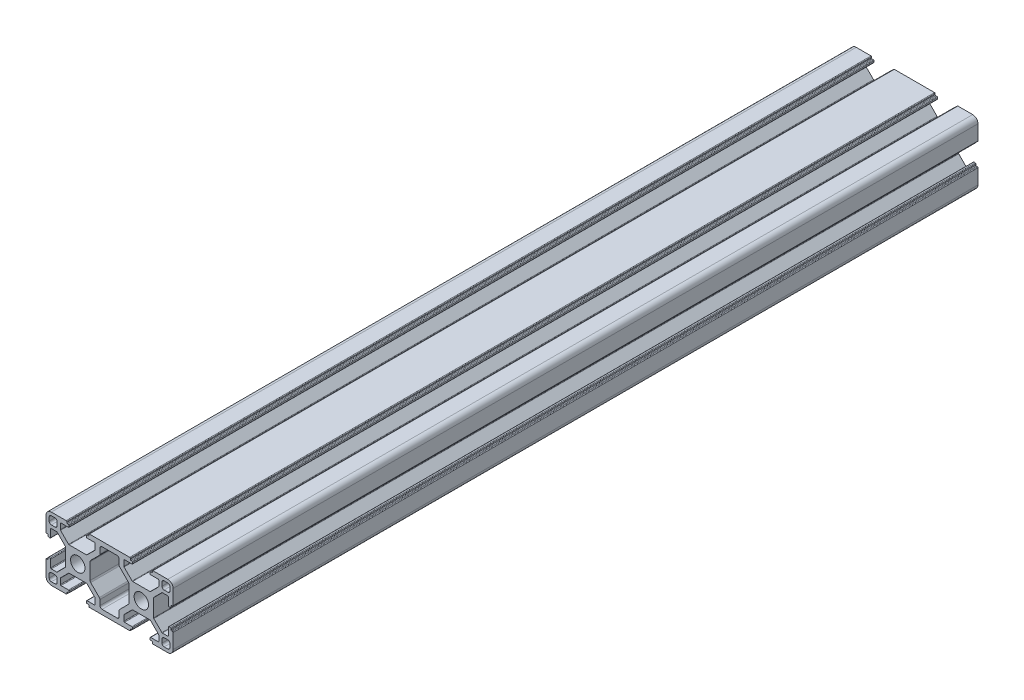
SolidWorks part; units mm, degrees
ref_plane "前视基准面" through (0, 0, 0) normal (0, 0, 1) x (1, 0, 0)
ref_plane "上视基准面" through (0, 0, 0) normal (0, 1, 0) x (1, 0, 0)
ref_plane "右视基准面" through (0, 0, 0) normal (1, 0, 0) x (0, 0, -1)
sketch "Model" plane through (0, 0, 0) normal (0, 0, 1) x (1, 0, 0)
  line L0 (154.3439, 58.7492) -> (156.0939, 58.7492)
  line L1 (157.0939, 57.7492) -> (157.0939, 55.9992)
  line L2 (156.0939, 54.9992) -> (154.3439, 54.9992)
  line L3 (153.3439, 55.9992) -> (153.3439, 57.7492)
  line L4 (102.8439, 58.7492) -> (101.0939, 58.7492)
  line L5 (100.0939, 57.7492) -> (100.0939, 55.9992)
  line L6 (101.0939, 54.9992) -> (102.8439, 54.9992)
  line L7 (103.8439, 55.9992) -> (103.8439, 57.7492)
  line L8 (147.9939, 59.2492) -> (148.4939, 59.2492)
  line L9 (148.7939, 59.5492) -> (148.7939, 59.9492)
  line L10 (149.0939, 60.2492) -> (156.0939, 60.2492)
  line L11 (158.5939, 57.7492) -> (158.5939, 50.7492)
  line L12 (158.2939, 50.4492) -> (157.8939, 50.4492)
  line L13 (157.5939, 50.1492) -> (157.5939, 49.6492)
  line L14 (157.2939, 49.3492) -> (156.6939, 49.3492)
  line L15 (156.3939, 49.6492) -> (156.3939, 53.1992)
  line L16 (156.0939, 53.4992) -> (153.5238, 53.4992)
  line L17 (153.3117, 53.4113) -> (149.4818, 49.5814)
  line L18 (149.3939, 49.3693) -> (149.3939, 45.2492)
  line L19 (149.3939, 45.2492) -> (149.3939, 41.1291)
  line L20 (149.4818, 40.9169) -> (153.3117, 37.087)
  line L21 (153.5238, 36.9992) -> (156.0939, 36.9992)
  line L22 (156.3939, 37.2992) -> (156.3939, 40.8492)
  line L23 (156.6939, 41.1492) -> (157.2939, 41.1492)
  line L24 (157.5939, 40.8492) -> (157.5939, 40.3492)
  line L25 (157.8939, 40.0492) -> (158.2939, 40.0492)
  line L26 (158.5939, 39.7492) -> (158.5939, 32.7492)
  line L27 (156.0939, 30.2492) -> (149.0939, 30.2492)
  line L28 (148.7939, 30.5492) -> (148.7939, 30.9492)
  line L29 (148.4939, 31.2492) -> (147.9939, 31.2492)
  line L30 (147.6939, 31.5492) -> (147.6939, 32.1492)
  line L31 (147.9939, 32.4492) -> (151.5439, 32.4492)
  line L32 (151.8439, 32.7492) -> (151.8439, 35.3193)
  line L33 (151.756, 35.5314) -> (147.9261, 39.3613)
  line L34 (147.714, 39.4492) -> (143.5939, 39.4492)
  line L35 (143.5939, 39.4492) -> (139.4738, 39.4492)
  line L36 (139.2617, 39.3613) -> (135.4318, 35.5314)
  line L37 (135.3439, 35.3193) -> (135.3439, 32.7492)
  line L38 (135.6439, 32.4492) -> (139.1939, 32.4492)
  line L39 (139.4939, 32.1492) -> (139.4939, 31.5492)
  line L40 (139.1939, 31.2492) -> (138.6939, 31.2492)
  line L41 (138.3939, 30.9492) -> (138.3939, 30.5492)
  line L42 (138.0939, 30.2492) -> (119.0939, 30.2492)
  line L43 (118.7939, 30.5492) -> (118.7939, 30.9492)
  line L44 (118.4939, 31.2492) -> (117.9939, 31.2492)
  line L45 (117.6939, 31.5492) -> (117.6939, 32.1492)
  line L46 (117.9939, 32.4492) -> (121.5439, 32.4492)
  line L47 (121.8439, 32.7492) -> (121.8439, 35.3193)
  line L48 (121.756, 35.5314) -> (117.9261, 39.3613)
  line L49 (117.714, 39.4492) -> (113.5939, 39.4492)
  line L50 (113.5939, 39.4492) -> (109.4738, 39.4492)
  line L51 (109.2617, 39.3613) -> (105.4318, 35.5314)
  line L52 (105.3439, 35.3193) -> (105.3439, 32.7492)
  line L53 (105.6439, 32.4492) -> (109.1939, 32.4492)
  line L54 (109.4939, 32.1492) -> (109.4939, 31.5492)
  line L55 (109.1939, 31.2492) -> (108.6939, 31.2492)
  line L56 (108.3939, 30.9492) -> (108.3939, 30.5492)
  line L57 (108.0939, 30.2492) -> (101.0939, 30.2492)
  line L58 (98.5939, 32.7492) -> (98.5939, 39.7492)
  line L59 (98.8939, 40.0492) -> (99.2939, 40.0492)
  line L60 (99.5939, 40.3492) -> (99.5939, 40.8492)
  line L61 (99.8939, 41.1492) -> (100.4939, 41.1492)
  line L62 (100.7939, 40.8492) -> (100.7939, 37.2992)
  line L63 (101.0939, 36.9992) -> (103.664, 36.9992)
  line L64 (103.8761, 37.087) -> (107.706, 40.9169)
  line L65 (107.7939, 41.1291) -> (107.7939, 45.2492)
  line L66 (107.7939, 45.2492) -> (107.7939, 49.3693)
  line L67 (107.706, 49.5814) -> (103.8761, 53.4113)
  line L68 (103.664, 53.4992) -> (101.0939, 53.4992)
  line L69 (100.7939, 53.1992) -> (100.7939, 49.6492)
  line L70 (100.4939, 49.3492) -> (99.8939, 49.3492)
  line L71 (99.5939, 49.6492) -> (99.5939, 50.1492)
  line L72 (99.2939, 50.4492) -> (98.8939, 50.4492)
  line L73 (98.5939, 50.7492) -> (98.5939, 57.7492)
  line L74 (101.0939, 60.2492) -> (108.0939, 60.2492)
  line L75 (108.3939, 59.9492) -> (108.3939, 59.5492)
  line L76 (108.6939, 59.2492) -> (109.1939, 59.2492)
  line L77 (109.4939, 58.9492) -> (109.4939, 58.3492)
  line L78 (109.1939, 58.0492) -> (105.6439, 58.0492)
  line L79 (105.3439, 57.7492) -> (105.3439, 55.1791)
  line L80 (105.4318, 54.9669) -> (109.2617, 51.137)
  line L81 (109.4738, 51.0492) -> (113.5939, 51.0492)
  line L82 (113.5939, 51.0492) -> (117.714, 51.0492)
  line L83 (117.9261, 51.137) -> (121.756, 54.9669)
  line L84 (121.8439, 55.1791) -> (121.8439, 57.7492)
  line L85 (121.5439, 58.0492) -> (117.9939, 58.0492)
  line L86 (117.6939, 58.3492) -> (117.6939, 58.9492)
  line L87 (117.9939, 59.2492) -> (118.4939, 59.2492)
  line L88 (118.7939, 59.5492) -> (118.7939, 59.9492)
  line L89 (119.0939, 60.2492) -> (138.0939, 60.2492)
  line L90 (138.3939, 59.9492) -> (138.3939, 59.5492)
  line L91 (138.6939, 59.2492) -> (139.1939, 59.2492)
  line L92 (139.4939, 58.9492) -> (139.4939, 58.3492)
  line L93 (139.1939, 58.0492) -> (135.6439, 58.0492)
  line L94 (135.3439, 57.7492) -> (135.3439, 55.1791)
  line L95 (135.4318, 54.9669) -> (139.2617, 51.137)
  line L96 (139.4738, 51.0492) -> (143.5939, 51.0492)
  line L97 (143.5939, 51.0492) -> (147.714, 51.0492)
  line L98 (147.9261, 51.137) -> (151.756, 54.9669)
  line L99 (151.8439, 55.1791) -> (151.8439, 57.7492)
  line L100 (151.5439, 58.0492) -> (147.9939, 58.0492)
  line L101 (147.6939, 58.3492) -> (147.6939, 58.9492)
  line L103 (154.3439, 31.7492) -> (156.0939, 31.7492)
  line L104 (157.0939, 32.7492) -> (157.0939, 34.4992)
  line L105 (156.0939, 35.4992) -> (154.3439, 35.4992)
  line L106 (153.3439, 34.4992) -> (153.3439, 32.7492)
  line L108 (119.3939, 49.0793) -> (119.3939, 45.2492)
  line L109 (119.3939, 45.2492) -> (119.3939, 41.419)
  line L110 (119.6868, 40.7119) -> (123.751, 36.6477)
  line L111 (124.0439, 35.9406) -> (124.0439, 33.4492)
  line L112 (125.0439, 32.4492) -> (128.5939, 32.4492)
  line L113 (128.5939, 32.4492) -> (132.1439, 32.4492)
  line L114 (133.1439, 33.4492) -> (133.1439, 35.9406)
  line L115 (133.4368, 36.6477) -> (137.501, 40.7119)
  line L116 (137.7939, 41.419) -> (137.7939, 45.2492)
  line L117 (137.7939, 45.2492) -> (137.7939, 49.0793)
  line L118 (137.501, 49.7864) -> (133.4368, 53.8507)
  line L119 (133.1439, 54.5578) -> (133.1439, 57.0492)
  line L120 (132.1439, 58.0492) -> (128.5939, 58.0492)
  line L121 (128.5939, 58.0492) -> (125.0439, 58.0492)
  line L122 (124.0439, 57.0492) -> (124.0439, 54.5578)
  line L123 (123.751, 53.8507) -> (119.6868, 49.7864)
  line L128 (102.8439, 31.7492) -> (101.0939, 31.7492)
  line L129 (100.0939, 32.7492) -> (100.0939, 34.4992)
  line L130 (101.0939, 35.4992) -> (102.8439, 35.4992)
  line L131 (103.8439, 34.4992) -> (103.8439, 32.7492)
  circle A0 centre (113.5939, 45.2492) radius 3.4
  circle A1 centre (143.5939, 45.2492) radius 3.4
  arc A2 (154.3439, 58.7492) -> (153.3439, 57.7492) centre (154.3439, 57.7492) ccw
  arc A3 (157.0939, 57.7492) -> (156.0939, 58.7492) centre (156.0939, 57.7492) ccw
  arc A4 (156.0939, 54.9992) -> (157.0939, 55.9992) centre (156.0939, 55.9992) ccw
  arc A5 (153.3439, 55.9992) -> (154.3439, 54.9992) centre (154.3439, 55.9992) ccw
  arc A6 (103.8439, 57.7492) -> (102.8439, 58.7492) centre (102.8439, 57.7492) ccw
  arc A7 (101.0939, 58.7492) -> (100.0939, 57.7492) centre (101.0939, 57.7492) ccw
  arc A8 (100.0939, 55.9992) -> (101.0939, 54.9992) centre (101.0939, 55.9992) ccw
  arc A9 (102.8439, 54.9992) -> (103.8439, 55.9992) centre (102.8439, 55.9992) ccw
  arc A10 (148.4939, 59.2492) -> (148.7939, 59.5492) centre (148.4939, 59.5492) ccw
  arc A11 (149.0939, 60.2492) -> (148.7939, 59.9492) centre (149.0939, 59.9492) ccw
  arc A12 (158.5939, 57.7492) -> (156.0939, 60.2492) centre (156.0939, 57.7492) ccw
  arc A13 (158.2939, 50.4492) -> (158.5939, 50.7492) centre (158.2939, 50.7492) ccw
  arc A14 (157.8939, 50.4492) -> (157.5939, 50.1492) centre (157.8939, 50.1492) ccw
  arc A15 (157.2939, 49.3492) -> (157.5939, 49.6492) centre (157.2939, 49.6492) ccw
  arc A16 (156.3939, 49.6492) -> (156.6939, 49.3492) centre (156.6939, 49.6492) ccw
  arc A17 (156.3939, 53.1992) -> (156.0939, 53.4992) centre (156.0939, 53.1992) ccw
  arc A18 (153.5238, 53.4992) -> (153.3117, 53.4113) centre (153.5238, 53.1992) ccw
  arc A19 (149.4818, 49.5814) -> (149.3939, 49.3693) centre (149.6939, 49.3693) ccw
  arc A20 (149.3939, 41.1291) -> (149.4818, 40.9169) centre (149.6939, 41.1291) ccw
  arc A21 (153.3117, 37.087) -> (153.5238, 36.9992) centre (153.5238, 37.2992) ccw
  arc A22 (156.0939, 36.9992) -> (156.3939, 37.2992) centre (156.0939, 37.2992) ccw
  arc A23 (156.6939, 41.1492) -> (156.3939, 40.8492) centre (156.6939, 40.8492) ccw
  arc A24 (157.5939, 40.8492) -> (157.2939, 41.1492) centre (157.2939, 40.8492) ccw
  arc A25 (157.5939, 40.3492) -> (157.8939, 40.0492) centre (157.8939, 40.3492) ccw
  arc A26 (158.5939, 39.7492) -> (158.2939, 40.0492) centre (158.2939, 39.7492) ccw
  arc A27 (156.0939, 30.2492) -> (158.5939, 32.7492) centre (156.0939, 32.7492) ccw
  arc A28 (148.7939, 30.5492) -> (149.0939, 30.2492) centre (149.0939, 30.5492) ccw
  arc A29 (148.7939, 30.9492) -> (148.4939, 31.2492) centre (148.4939, 30.9492) ccw
  arc A30 (147.6939, 31.5492) -> (147.9939, 31.2492) centre (147.9939, 31.5492) ccw
  arc A31 (147.9939, 32.4492) -> (147.6939, 32.1492) centre (147.9939, 32.1492) ccw
  arc A32 (151.5439, 32.4492) -> (151.8439, 32.7492) centre (151.5439, 32.7492) ccw
  arc A33 (151.8439, 35.3193) -> (151.756, 35.5314) centre (151.5439, 35.3193) ccw
  arc A34 (147.9261, 39.3613) -> (147.714, 39.4492) centre (147.714, 39.1492) ccw
  arc A35 (139.4738, 39.4492) -> (139.2617, 39.3613) centre (139.4738, 39.1492) ccw
  arc A36 (135.4318, 35.5314) -> (135.3439, 35.3193) centre (135.6439, 35.3193) ccw
  arc A37 (135.3439, 32.7492) -> (135.6439, 32.4492) centre (135.6439, 32.7492) ccw
  arc A38 (139.4939, 32.1492) -> (139.1939, 32.4492) centre (139.1939, 32.1492) ccw
  arc A39 (139.1939, 31.2492) -> (139.4939, 31.5492) centre (139.1939, 31.5492) ccw
  arc A40 (138.6939, 31.2492) -> (138.3939, 30.9492) centre (138.6939, 30.9492) ccw
  arc A41 (138.0939, 30.2492) -> (138.3939, 30.5492) centre (138.0939, 30.5492) ccw
  arc A42 (118.7939, 30.5492) -> (119.0939, 30.2492) centre (119.0939, 30.5492) ccw
  arc A43 (118.7939, 30.9492) -> (118.4939, 31.2492) centre (118.4939, 30.9492) ccw
  arc A44 (117.6939, 31.5492) -> (117.9939, 31.2492) centre (117.9939, 31.5492) ccw
  arc A45 (117.9939, 32.4492) -> (117.6939, 32.1492) centre (117.9939, 32.1492) ccw
  arc A46 (121.5439, 32.4492) -> (121.8439, 32.7492) centre (121.5439, 32.7492) ccw
  arc A47 (121.8439, 35.3193) -> (121.756, 35.5314) centre (121.5439, 35.3193) ccw
  arc A48 (117.9261, 39.3613) -> (117.714, 39.4492) centre (117.714, 39.1492) ccw
  arc A49 (109.4738, 39.4492) -> (109.2617, 39.3613) centre (109.4738, 39.1492) ccw
  arc A50 (105.4318, 35.5314) -> (105.3439, 35.3193) centre (105.6439, 35.3193) ccw
  arc A51 (105.3439, 32.7492) -> (105.6439, 32.4492) centre (105.6439, 32.7492) ccw
  arc A52 (109.4939, 32.1492) -> (109.1939, 32.4492) centre (109.1939, 32.1492) ccw
  arc A53 (109.1939, 31.2492) -> (109.4939, 31.5492) centre (109.1939, 31.5492) ccw
  arc A54 (108.6939, 31.2492) -> (108.3939, 30.9492) centre (108.6939, 30.9492) ccw
  arc A55 (108.0939, 30.2492) -> (108.3939, 30.5492) centre (108.0939, 30.5492) ccw
  arc A56 (98.5939, 32.7492) -> (101.0939, 30.2492) centre (101.0939, 32.7492) ccw
  arc A57 (98.8939, 40.0492) -> (98.5939, 39.7492) centre (98.8939, 39.7492) ccw
  arc A58 (99.2939, 40.0492) -> (99.5939, 40.3492) centre (99.2939, 40.3492) ccw
  arc A59 (99.8939, 41.1492) -> (99.5939, 40.8492) centre (99.8939, 40.8492) ccw
  arc A60 (100.7939, 40.8492) -> (100.4939, 41.1492) centre (100.4939, 40.8492) ccw
  arc A61 (100.7939, 37.2992) -> (101.0939, 36.9992) centre (101.0939, 37.2992) ccw
  arc A62 (103.664, 36.9992) -> (103.8761, 37.087) centre (103.664, 37.2992) ccw
  arc A63 (107.706, 40.9169) -> (107.7939, 41.1291) centre (107.4939, 41.1291) ccw
  arc A64 (107.7939, 49.3693) -> (107.706, 49.5814) centre (107.4939, 49.3693) ccw
  arc A65 (103.8761, 53.4113) -> (103.664, 53.4992) centre (103.664, 53.1992) ccw
  arc A66 (101.0939, 53.4992) -> (100.7939, 53.1992) centre (101.0939, 53.1992) ccw
  arc A67 (100.4939, 49.3492) -> (100.7939, 49.6492) centre (100.4939, 49.6492) ccw
  arc A68 (99.5939, 49.6492) -> (99.8939, 49.3492) centre (99.8939, 49.6492) ccw
  arc A69 (99.5939, 50.1492) -> (99.2939, 50.4492) centre (99.2939, 50.1492) ccw
  arc A70 (98.5939, 50.7492) -> (98.8939, 50.4492) centre (98.8939, 50.7492) ccw
  arc A71 (101.0939, 60.2492) -> (98.5939, 57.7492) centre (101.0939, 57.7492) ccw
  arc A72 (108.3939, 59.9492) -> (108.0939, 60.2492) centre (108.0939, 59.9492) ccw
  arc A73 (108.3939, 59.5492) -> (108.6939, 59.2492) centre (108.6939, 59.5492) ccw
  arc A74 (109.4939, 58.9492) -> (109.1939, 59.2492) centre (109.1939, 58.9492) ccw
  arc A75 (109.1939, 58.0492) -> (109.4939, 58.3492) centre (109.1939, 58.3492) ccw
  arc A76 (105.6439, 58.0492) -> (105.3439, 57.7492) centre (105.6439, 57.7492) ccw
  arc A77 (105.3439, 55.1791) -> (105.4318, 54.9669) centre (105.6439, 55.1791) ccw
  arc A78 (109.2617, 51.137) -> (109.4738, 51.0492) centre (109.4738, 51.3492) ccw
  arc A79 (117.714, 51.0492) -> (117.9261, 51.137) centre (117.714, 51.3492) ccw
  arc A80 (121.756, 54.9669) -> (121.8439, 55.1791) centre (121.5439, 55.1791) ccw
  arc A81 (121.8439, 57.7492) -> (121.5439, 58.0492) centre (121.5439, 57.7492) ccw
  arc A82 (117.6939, 58.3492) -> (117.9939, 58.0492) centre (117.9939, 58.3492) ccw
  arc A83 (117.9939, 59.2492) -> (117.6939, 58.9492) centre (117.9939, 58.9492) ccw
  arc A84 (118.4939, 59.2492) -> (118.7939, 59.5492) centre (118.4939, 59.5492) ccw
  arc A85 (119.0939, 60.2492) -> (118.7939, 59.9492) centre (119.0939, 59.9492) ccw
  arc A86 (138.3939, 59.9492) -> (138.0939, 60.2492) centre (138.0939, 59.9492) ccw
  arc A87 (138.3939, 59.5492) -> (138.6939, 59.2492) centre (138.6939, 59.5492) ccw
  arc A88 (139.4939, 58.9492) -> (139.1939, 59.2492) centre (139.1939, 58.9492) ccw
  arc A89 (139.1939, 58.0492) -> (139.4939, 58.3492) centre (139.1939, 58.3492) ccw
  arc A90 (135.6439, 58.0492) -> (135.3439, 57.7492) centre (135.6439, 57.7492) ccw
  arc A91 (135.3439, 55.1791) -> (135.4318, 54.9669) centre (135.6439, 55.1791) ccw
  arc A92 (139.2617, 51.137) -> (139.4738, 51.0492) centre (139.4738, 51.3492) ccw
  arc A93 (147.714, 51.0492) -> (147.9261, 51.137) centre (147.714, 51.3492) ccw
  arc A94 (151.756, 54.9669) -> (151.8439, 55.1791) centre (151.5439, 55.1791) ccw
  arc A95 (151.8439, 57.7492) -> (151.5439, 58.0492) centre (151.5439, 57.7492) ccw
  arc A96 (147.6939, 58.3492) -> (147.9939, 58.0492) centre (147.9939, 58.3492) ccw
  arc A97 (147.9939, 59.2492) -> (147.6939, 58.9492) centre (147.9939, 58.9492) ccw
  arc A98 (153.3439, 32.7492) -> (154.3439, 31.7492) centre (154.3439, 32.7492) ccw
  arc A99 (156.0939, 31.7492) -> (157.0939, 32.7492) centre (156.0939, 32.7492) ccw
  arc A100 (157.0939, 34.4992) -> (156.0939, 35.4992) centre (156.0939, 34.4992) ccw
  arc A101 (154.3439, 35.4992) -> (153.3439, 34.4992) centre (154.3439, 34.4992) ccw
  arc A102 (119.6868, 49.7864) -> (119.3939, 49.0793) centre (120.3939, 49.0793) ccw
  arc A103 (119.3939, 41.419) -> (119.6868, 40.7119) centre (120.3939, 41.419) ccw
  arc A104 (124.0439, 35.9406) -> (123.751, 36.6477) centre (123.0439, 35.9406) ccw
  arc A105 (124.0439, 33.4492) -> (125.0439, 32.4492) centre (125.0439, 33.4492) ccw
  arc A106 (132.1439, 32.4492) -> (133.1439, 33.4492) centre (132.1439, 33.4492) ccw
  arc A107 (133.4368, 36.6477) -> (133.1439, 35.9406) centre (134.1439, 35.9406) ccw
  arc A108 (137.501, 40.7119) -> (137.7939, 41.419) centre (136.7939, 41.419) ccw
  arc A109 (137.7939, 49.0793) -> (137.501, 49.7864) centre (136.7939, 49.0793) ccw
  arc A110 (133.1439, 54.5578) -> (133.4368, 53.8507) centre (134.1439, 54.5578) ccw
  arc A111 (133.1439, 57.0492) -> (132.1439, 58.0492) centre (132.1439, 57.0492) ccw
  arc A112 (125.0439, 58.0492) -> (124.0439, 57.0492) centre (125.0439, 57.0492) ccw
  arc A113 (123.751, 53.8507) -> (124.0439, 54.5578) centre (123.0439, 54.5578) ccw
  arc A114 (102.8439, 31.7492) -> (103.8439, 32.7492) centre (102.8439, 32.7492) ccw
  arc A115 (100.0939, 32.7492) -> (101.0939, 31.7492) centre (101.0939, 32.7492) ccw
  arc A116 (101.0939, 35.4992) -> (100.0939, 34.4992) centre (101.0939, 34.4992) ccw
  arc A117 (103.8439, 34.4992) -> (102.8439, 35.4992) centre (102.8439, 34.4992) ccw
extrude "凸台-拉伸1" add sketch "Model" along normal blind 380
